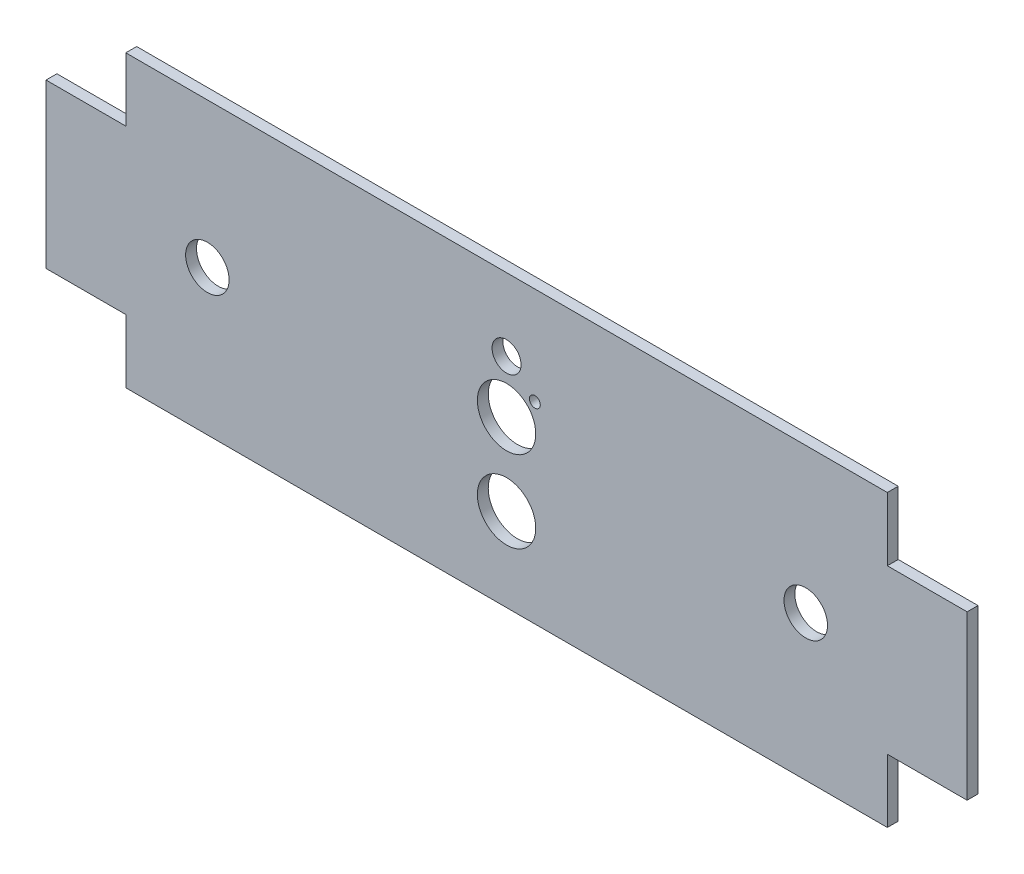
SolidWorks part; units mm, degrees
ref_plane "Alzado" through (0, 0, 0) normal (0, 0, 1) x (1, 0, 0)
ref_plane "Planta" through (0, 0, 0) normal (0, 1, 0) x (1, 0, 0)
ref_plane "Vista lateral" through (0, 0, 0) normal (1, 0, 0) x (0, 0, -1)
sketch "Croquis1" plane through (0, 0, 0) normal (0, 0, 1) x (1, 0, 0)
  line L0 (0, 0) -> (-116, 0) construction
  line L1 (105, -30) -> (-105, -30)
  line L2 (105, -30) -> (105, 30)
  line L3 (105, 30) -> (-105, 30)
  line L4 (-105, -30) -> (-105, 30)
  line L5 (105, -30) -> (-105, 30) construction
  line L6 (105, 30) -> (-105, -30) construction
  line L7 (0, 0) -> (116, 0) construction
  line L8 (-127, -22.5) -> (-105, -22.5)
  line L9 (-127, -22.5) -> (-127, 22.5)
  line L10 (-127, 22.5) -> (-105, 22.5)
  line L11 (-105, -22.5) -> (-105, 22.5)
  line L12 (-127, -22.5) -> (-105, 22.5) construction
  line L13 (-127, 22.5) -> (-105, -22.5) construction
  line L15 (127, 22.5) -> (105, 22.5)
  line L16 (127, 22.5) -> (127, -22.5)
  line L17 (127, -22.5) -> (105, -22.5)
  line L18 (105, 22.5) -> (105, -22.5)
  line L19 (127, 22.5) -> (105, -22.5) construction
  line L20 (127, -22.5) -> (105, 22.5) construction
  point P0 (0, 0)
  dimension "D1" = 210
  dimension "D2" = 60
  dimension "D3" = 45
  dimension "D4" = 22
  dimension "D5" = 22
  dimension "D6" = 45
extrude "Saliente-Extruir1" add sketch "Croquis1" along normal blind 3 contours L10 L9 L8 L4 | L4 L1 L2 L3 | L16 L17 L18 L15
sketch "Croquis2" plane through (0, 0, 3) normal (0, 0, 1) x (1, 0, 0)
  line L0 (0, 0) -> (-82.5, 0) construction
  line L3 (82.5, 0) -> (0, 0) construction
  circle A0 centre (82.5, 0) radius 6
  circle A1 centre (-82.5, 0) radius 6
  dimension "D2" = 12
  dimension "D1" = 165
extrude "Cortar-Extruir1" cut sketch "Croquis2" against normal up to next
sketch "Croquis3" plane through (0, 0, 3) normal (0, 0, 1) x (1, 0, 0)
  line L0 (0, 0) -> (0, 20) construction
  circle A0 centre (0, 20) radius 4
  dimension "D1" = 8
  dimension "D2" = 20
extrude "Cortar-Extruir2" cut sketch "Croquis3" against normal up to next
sketch "Croquis4" plane through (0, 0, 3) normal (0, 0, 1) x (1, 0, 0)
  line L0 (105, -30) -> (105, -22.5) construction
  line L1 (-105, -30) -> (105, -30)
  line L2 (-105, -30) -> (-105, -40)
  line L3 (-105, -40) -> (105, -40)
  line L4 (105, -30) -> (105, -40)
  dimension "D1" = 10
extrude "Saliente-Extruir2" add sketch "Croquis4" against normal up to surface (3 mm away) up to face at (4, 20, 0)
sketch "Croquis5" plane through (0, 0, 3) normal (0, 0, 1) x (1, 0, 0)
  line L0 (105, 22.5) -> (105, 30) construction
  line L1 (-105, 30) -> (105, 30)
  line L2 (-105, 30) -> (-105, 40)
  line L3 (-105, 40) -> (105, 40)
  line L4 (105, 30) -> (105, 40)
  dimension "D1" = 10
extrude "Saliente-Extruir3" add sketch "Croquis5" against normal up to surface (3 mm away) up to face at (4, 20, 0)
sketch "Croquis6" plane through (0, 0, 0) normal (0, 0, -1) x (-1, 0, 0)
  line L0 (0, 20) -> (0, 5.5) construction
  line L1 (0, 5.5) -> (-7.8, 5.5) construction
  line L2 (-7.8, 5.5) -> (-7.8, 13.05) construction
  line L3 (0, 5.5) -> (0, -17) construction
  circle A0 centre (-7.8, 13.05) radius 1.5
  circle A1 centre (0, 5.5) radius 8.05
  circle A2 centre (0, -17) radius 8.05
  circle A3 centre (0, 20) radius 4 construction
  circle A4 centre (0, 20) radius 4 construction
  dimension "D1" = 3
  dimension "D4" = 16.1
  dimension "D2" = 7.8
  dimension "D3" = 7.55
  dimension "D5" = 14.5
  dimension "D6" = 22.5
extrude "Cortar-Extruir3" cut sketch "Croquis6" against normal blind 7
